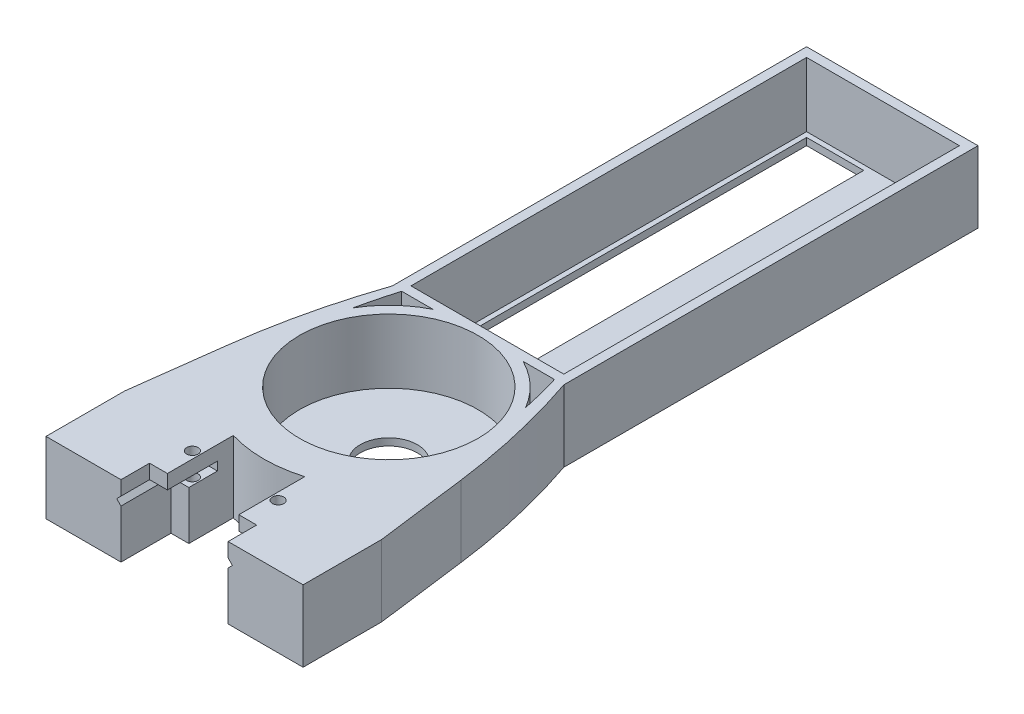
SolidWorks part; units mm, degrees
material "ABS"
ref_plane "Plano frontal" through (0, 0, 0) normal (0, 0, 1) x (1, 0, 0)
ref_plane "Plano superior" through (0, 0, 0) normal (0, 1, 0) x (1, 0, 0)
ref_plane "Plano direito" through (0, 0, 0) normal (1, 0, 0) x (0, 0, -1)
other "Centro da massa"
sketch "Esboço1" plane through (0, 0, 0) normal (0, 0, 1) x (1, 0, 0)
  line L0 (0, 0) -> (0, 1.8808) construction
  line L3 (-5, 1.8) -> (-5, -5)
  line L4 (-5, -5) -> (-14.1, -5)
  line L5 (-14.1, -5) -> (-14.1, 5)
  line L6 (-14.1, 5) -> (-5, 5)
  line L7 (-5, 5) -> (-5, 3)
  line L8 (0, 0) -> (-1.0783, 0) construction
  line L9 (-5, 3) -> (-7.5, 3)
  line L10 (-7.5, 3) -> (-8.1, 2.4)
  line L11 (-8.1, 2.4) -> (-7.5, 1.8)
  line L12 (-7.5, 1.8) -> (-5, 1.8)
  line L13 (7.5, 1.8) -> (5, 1.8)
  line L14 (8.1, 2.4) -> (7.5, 1.8)
  line L15 (7.5, 3) -> (8.1, 2.4)
  line L16 (5, 3) -> (7.5, 3)
  line L17 (5, 5) -> (5, 3)
  line L18 (14.1, 5) -> (5, 5)
  line L19 (14.1, -5) -> (14.1, 5)
  line L20 (5, -5) -> (14.1, -5)
  line L21 (5, 1.8) -> (5, -5)
  point P4 (0, 0)
  point P13 (0, 0)
  point P15 (-6.5, 1.5991)
  point P25 (-6.5, 5)
  point P26 (-6.5, 1.6055)
  dimension "D1" = 1.2
  dimension "D2" = 10
  dimension "D3" = 10
  dimension "D4" = 6
  dimension "D5" = 15
  dimension "D6" = 2
extrude "Ressalto-extrusão1" add sketch "Esboço1" along normal blind 11
sketch "Esboço3" plane through (0, 0, 0) normal (0, 1, 0) x (1, 0, 0)
  line L0 (-14.1, 0) -> (-5, 0)
  line L1 (-5, 0) -> (-5, 2.2295)
  line L2 (5, 2.2295) -> (5, 0)
  line L3 (5, 0) -> (14.1, 0)
  line L4 (18, 0) -> (16.3534, 12.7698)
  line L5 (0, 0) -> (0, 12.5561) construction
  line L6 (-18, 0) -> (-16.3534, 12.7698)
  line L7 (12, 31.5) -> (12, 89.5)
  line L8 (12, 89.5) -> (-12, 89.5)
  line L9 (-12, 31.5) -> (-12, 89.5)
  line L10 (0, 31.5) -> (0, 89.5) construction
  line L11 (10, 89.5) -> (10, 87.5) construction
  line L12 (-10, 87.5) -> (10, 87.5)
  line L13 (-10, 87.5) -> (-10, 33.5)
  line L14 (-10, 33.5) -> (10, 33.5)
  line L15 (10, 87.5) -> (10, 33.5)
  line L16 (-10, 87.5) -> (10, 33.5) construction
  line L17 (-10, 33.5) -> (10, 87.5) construction
  line L18 (10, 87.5) -> (12, 87.5) construction
  line L19 (2, 87.5) -> (2, 33.5)
  line L20 (19.3125, 41.5) -> (19.3125, 87.5) construction
  line L21 (-2, 87.5) -> (-2, 33.5)
  line L23 (18, 0) -> (18, -11)
  line L24 (18, -11) -> (14.1, -11)
  line L25 (14.1, -11) -> (14.1, 0)
  line L27 (-14.1, -11) -> (-14.1, 0)
  line L28 (-18, -11) -> (-14.1, -11)
  line L29 (-18, 0) -> (-18, -11)
  circle A0 centre (0, 19) radius 12.5
  arc A1 (-5, 2.2295) -> (5, 2.2295) centre (0, 19) ccw
  arc A4 (16.3534, 12.7698) -> (12, 31.5) centre (-79.0326, 0.4704) ccw
  arc A5 (-16.3534, 12.7698) -> (-12, 31.5) centre (79.0326, 0.4704) cw
  point P9 (16.2889, 13.6029)
  point P21 (0, 60.5)
  point P36 (12, 30.7523)
  point P46 (17.0208, 15.9326)
  point P47 (0, 0)
  dimension "D1" = 25
  dimension "D4" = 10
  dimension "D5" = 24
  dimension "D6" = 2
  dimension "D2" = 19
  dimension "D7" = 46
  dimension "D8" = 22.5
  dimension "D3" = 5
  dimension "D9" = 2.5
  dimension "D11" = 36
  dimension "D10" = 4
extrude "Ressalto-extrusão2" add sketch "Esboço3" along normal through all from surface at -5 contours L12 L21 L14 L19 | L9 A5 L6 L0 L1 A1 L2 L3 L4 A4 L7 L8 L12 L15 L14 L13 A0
sketch "Esboço8" plane through (0, 5, 0) normal (0, 1, 0) x (1, 0, 0)
  point P0 (0, 19)
sketch "Esboço4" plane through (0, 5, 0) normal (0, 1, 0) x (1, 0, 0)
  line L5 (-10.7, 89.5) -> (-10.7, 88.2) construction
  line L6 (-10.7, 88.2) -> (10.7, 88.2)
  line L7 (-10.7, 88.2) -> (-10.7, 32.8)
  line L8 (-10.7, 32.8) -> (10.7, 32.8)
  line L9 (10.7, 88.2) -> (10.7, 32.8)
  line L11 (0, 89.5) -> (0, 79.7531) construction
  line L12 (-10.7, 88.2) -> (-12, 88.2) construction
  line L14 (-10, 33.5) -> (-10.7, 33.5) construction
  line L15 (-12, 31.5) -> (-12, 89.5) construction
  line L16 (-10, 32.8) -> (-10, 33.5) construction
  line L17 (12, 89.5) -> (-12, 89.5) construction
  point P7 (-12, 93.9959)
  point P14 (-10.5, 95.5)
  point P21 (0, 95.5)
  point P22 (-9, 38.5)
  dimension "D1" = 1.3
extrude "Corte-extrusão1" cut sketch "Esboço4" against normal offset from surface (9 mm away) 1
sketch "Esboço5" plane through (0, -5, 0) normal (0, -1, 0) x (1, 0, 0)
  line L0 (-7.5, 11) -> (-7.5, 4)
  line L1 (-18, 11) -> (-5, 11) construction
  line L2 (-7.5, 4) -> (-5, 4)
  line L3 (-5, 11) -> (-5, -2.2295) construction
  line L4 (-18, 0) -> (-5, 0) construction
  line L5 (-7.5, 11) -> (-5, 11)
  line L6 (-5, 11) -> (-5, 4)
  line L7 (0, 0) -> (0, 9.6435) construction
  line L8 (5, 11) -> (5, 4)
  line L9 (7.5, 11) -> (5, 11)
  line L10 (7.5, 4) -> (5, 4)
  line L11 (7.5, 11) -> (7.5, 4)
  dimension "D1" = 4
extrude "Corte-extrusão2" cut sketch "Esboço5" against normal up to next
sketch "Esboço6" plane through (0, 5, 0) normal (0, 1, 0) x (1, 0, 0)
  line L0 (0, 0) -> (0, -11.0885) construction
  line L2 (-5, -11) -> (-18, -11) construction
  line L3 (-7.5, -11) -> (7.5, -11)
  line L4 (-7.5, -11) -> (-7.5, -7)
  line L5 (-7.5, -7) -> (7.5, -7)
  line L6 (7.5, -11) -> (7.5, -7)
  circle A0 centre (-6, -2.5) radius 0.8
  circle A1 centre (6, -2.5) radius 0.8
  point P15 (0, 0)
  point P17 (0, 0)
  dimension "D3" = 1.6
  dimension "D1" = 12
  dimension "D2" = 2.5
  dimension "D4" = 21.5
  dimension "D5" = 4
extrude "Corte-extrusão3" cut sketch "Esboço6" against normal through all
sketch "Esboço9" plane through (0, 5, 0) normal (0, 1, 0) x (1, 0, 0)
  line L1 (6.3048, 31.5) -> (10.7, 31.5)
  line L3 (0, 19) -> (0, 41.0279) construction
  line L4 (-6.3048, 31.5) -> (-10.7, 31.5)
  line L5 (10.7, 32.8) -> (-10.7, 32.8) construction
  arc A0 (12.0933, 26.0534) -> (10.7, 31.5) centre (-65.8479, 9.0159) ccw
  arc A2 (-12.0933, 26.0534) -> (-6.3048, 31.5) centre (0, 19) cw
  arc A3 (-12.0933, 26.0534) -> (-10.7, 31.5) centre (65.8479, 9.0159) cw
  arc A14 (14, 19) -> (14, 19) centre (0, 19) ccw
  arc A15 (12.0933, 26.0534) -> (6.3048, 31.5) centre (0, 19) ccw
  point P0 (-12.5, 26.3472)
  dimension "D2" = 1.3
  dimension "D3" = 1.3
  dimension "D1" = 1.5
extrude "Corte-extrusão4" cut sketch "Esboço9" against normal through all both and the other way through all
sketch "Esboço10" plane through (0, -5, 0) normal (0, -1, 0) x (1, 0, 0)
  circle A0 centre (0, -19) radius 12.5
  circle A1 centre (0, -19) radius 4
  circle A2 centre (0, -19) radius 12.5 construction
  dimension "D1" = 8
extrude "Ressalto-extrusão3" add sketch "Esboço10" against normal blind 1
equation "\"D10@Esboço3\"=2*\"D6@Esboço3\""
